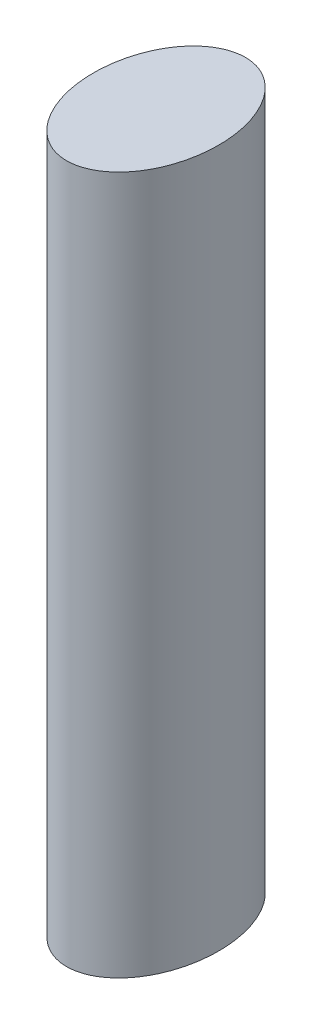
SolidWorks part; units mm, degrees
ref_plane "Front Plane" through (0, 0, 0) normal (0, 0, 1) x (1, 0, 0)
ref_plane "Top Plane" through (0, 0, 0) normal (0, 1, 0) x (1, 0, 0)
ref_plane "Right Plane" through (0, 0, 0) normal (1, 0, 0) x (0, 0, -1)
sketch "Sketch2" plane through (0, 0, 0) normal (0, 1, 0) x (1, 0, 0)
  ellipse E0 centre (0, 0) end of major axis (0, 25) minor radius 17.5
  dimension "D1" = 50
  dimension "D2" = 35
extrude "Boss-Extrude1" add sketch "Sketch2" along normal blind 195
